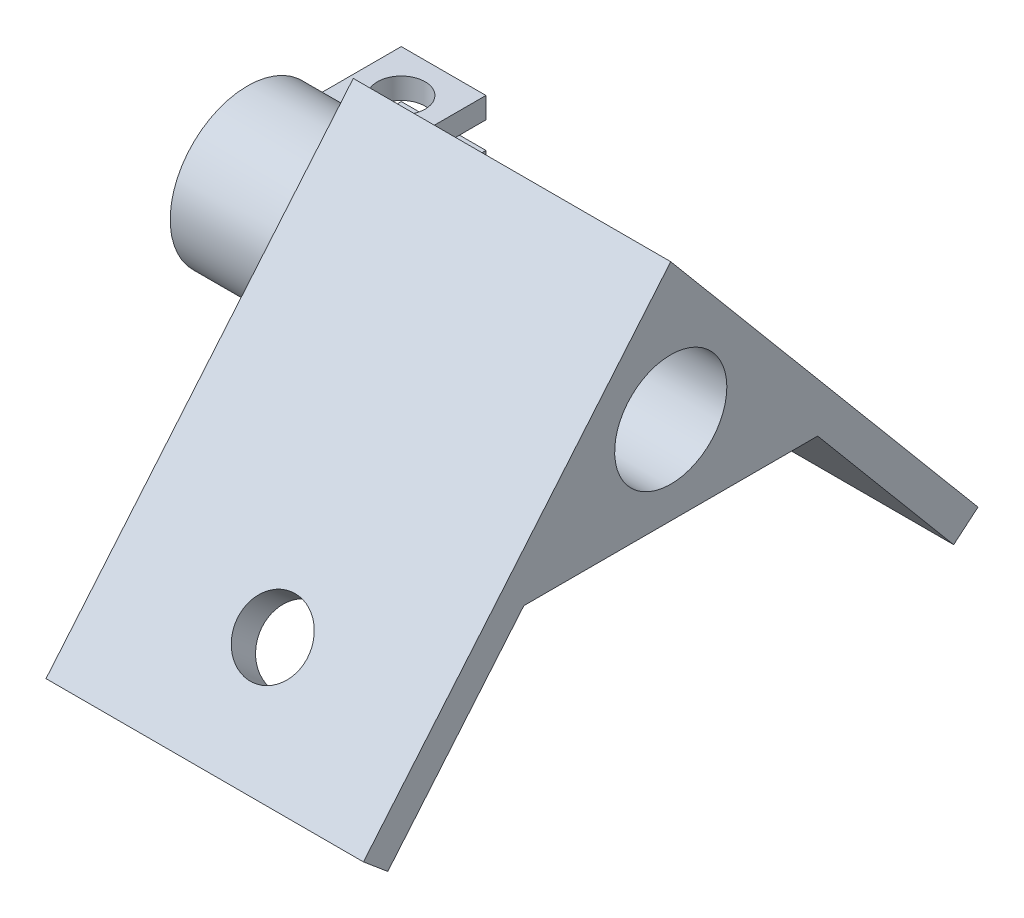
SolidWorks part; units mm, degrees
material "PLA Black"
ref_plane "Front" through (0, 0, 0) normal (0, 0, 1) x (1, 0, 0)
ref_plane "Top" through (0, 0, 0) normal (0, 1, 0) x (1, 0, 0)
ref_plane "Right" through (0, 0, 0) normal (1, 0, 0) x (0, 0, -1)
sketch "Sketch1" plane through (0, 0, 0) normal (1, 0, 0) x (0, 0, -1)
  line L0 (0, 12.9125) -> (-29.0371, -21.6925)
  line L1 (-29.0371, -21.6925) -> (-26.7389, -23.6209)
  line L2 (-26.7389, -23.6209) -> (-13.8832, -8.3)
  line L3 (-13.8832, -8.3) -> (13.8832, -8.3)
  line L4 (0, 31.2499) -> (0, -31.1028) construction
  line L5 (26.7389, -23.6209) -> (13.8832, -8.3)
  line L6 (0, 12.9125) -> (29.0371, -21.6925)
  line L7 (29.0371, -21.6925) -> (26.7389, -23.6209)
  circle A0 centre (0, 0) radius 5.3
  dimension "D1" = 10.6
  dimension "D4" = 3
  dimension "D2" = 40
  dimension "D3" = 3
  dimension "D5" = 3
  dimension "D6" = 20
extrude "Boss-Extrude1" add sketch "Sketch1" along normal mid plane 30
hole_wizard "M6 Clearance Hole1" positions "Sketch3" profile "Sketch4" hole size "M6" standard "DIN" end condition through all
sketch "Sketch3" plane through (0, 3.4068, 4.06) normal (0, -0.6428, -0.766) x (-1, 0, 0)
  line L0 (-34.564, -25.2821) -> (6.8322, -25.2821) construction
  line L2 (0, -15.2821) -> (0, -35.2821) construction
  line L3 (-15, -15.2821) -> (15, -15.2821) construction
  line L4 (-15, -35.2821) -> (15, -35.2821) construction
  point P0 (0, -25.2821)
sketch "Sketch4" plane through (0, -15.9604, 20.3111) normal (1, 0, 0) x (0, 0.766, -0.6428)
  line L0 (0, 0) -> (0, 25.2437)
  line L1 (0, 25.2437) -> (3.3, 25.2437)
  line L2 (3.3, 25.2437) -> (3.3, 0)
  line L5 (3.3, 0) -> (0, 0)
  line L11 (0, -6.35) -> (0, 107.95) construction
  dimension "Thru Hole Dia." = 6.6
  dimension "Thru Hole Depth" = 25.2437
mirror "Mirror1" about plane through (0, 0, 0) normal (0, 0, 1) of "M6 Clearance Hole1"
sketch "Sketch7" plane through (-15, 0, 0) normal (-1, 0, 0) x (0, 0, 1)
  line L0 (-5.1505, 1.25) -> (-7.1922, 1.25)
  line L1 (-5.1505, -1.25) -> (-7.1922, -1.25)
  line L2 (0, 0) -> (-15.3745, 0) construction
  arc A0 (-5.1505, -1.25) -> (-5.1505, 1.25) centre (0, 0) ccw
  arc A1 (-7.1922, -1.25) -> (-7.1922, 1.25) centre (0, 0) ccw
  circle A2 centre (0, 0) radius 5.3 construction
  dimension "D1" = 2
  dimension "D2" = 2.5
extrude "Boss-Extrude3" add sketch "Sketch7" along normal blind 2
sketch "Sketch5" plane through (-17, 0, 0) normal (-1, 0, 0) x (0, 0, 1)
  line L0 (-5.1505, 1.25) -> (-14.5366, 1.25)
  line L1 (-14.5366, 1.25) -> (-14.5366, 3.25)
  line L2 (-14.5366, 3.25) -> (-6.5366, 3.25)
  line L3 (0, 0) -> (-16.2155, 0) construction
  line L4 (-6.5366, -3.25) -> (-6.5366, -10.25)
  line L5 (-14.5366, -1.25) -> (-14.5366, -10.25)
  line L6 (-5.1505, -1.25) -> (-14.5366, -1.25)
  line L7 (-6.5366, -10.25) -> (-14.5366, -10.25)
  circle A0 centre (0, 0) radius 5.3 construction
  arc A1 (-6.5366, 3.25) -> (-6.5366, -3.25) centre (0, 0) cw
  arc A2 (-5.1505, 1.25) -> (-5.1505, -1.25) centre (0, 0) cw
  dimension "D1" = 2
  dimension "D2" = 8
  dimension "D3" = 2.5
  dimension "D4" = 2
  dimension "D5" = 9
extrude "Boss-Extrude2" add sketch "Sketch5" along normal blind 8
sketch "Sketch6" plane through (0, 3.25, 0) normal (0, 1, 0) x (1, 0, 0)
  line L0 (-21, 14.5366) -> (-21, 6.5366) construction
  line L1 (-25, 14.5366) -> (-17, 14.5366) construction
  line L2 (-25, 6.5366) -> (-17, 6.5366) construction
  circle A0 centre (-21, 10.5366) radius 2.25
  dimension "D1" = 4.5
extrude "Cut-Extrude1" cut sketch "Sketch6" against normal through all
